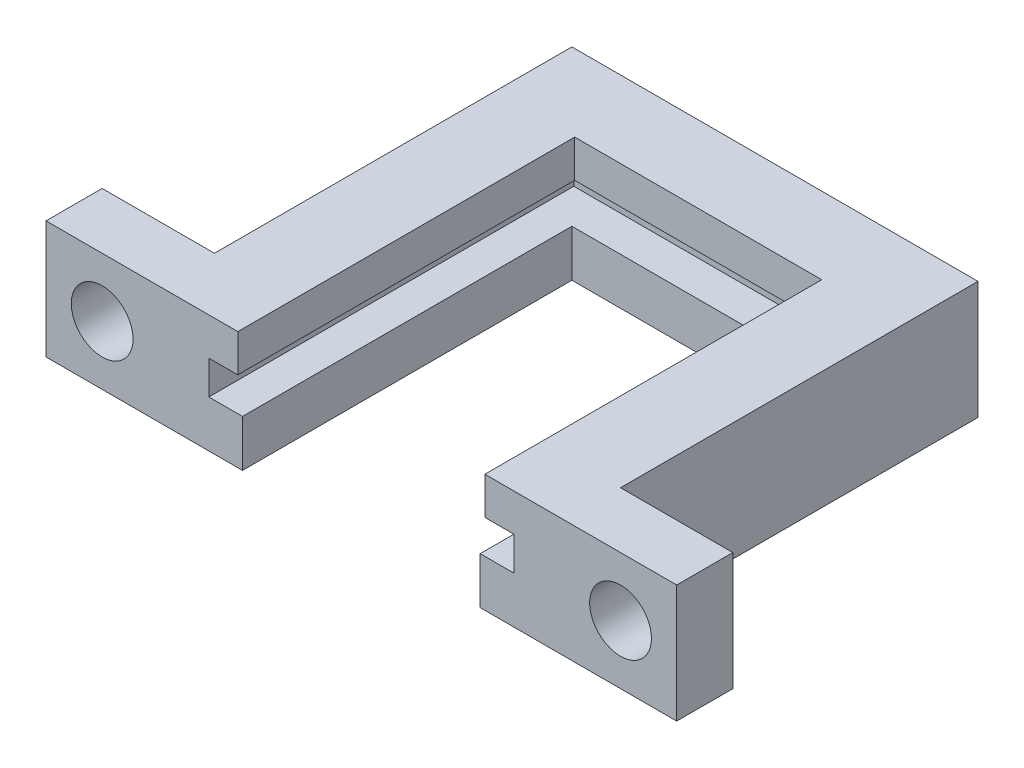
SolidWorks part; units mm, degrees
ref_plane "Front Plane" through (0, 0, 0) normal (0, 0, 1) x (1, 0, 0)
ref_plane "Top Plane" through (0, 0, 0) normal (0, 1, 0) x (1, 0, 0)
ref_plane "Right Plane" through (0, 0, 0) normal (1, 0, 0) x (0, 0, -1)
sketch "Sketch1" plane through (0, 0, 0) normal (0, 1, 0) x (1, 0, 0)
  line L0 (0, 0) -> (0, 22.1)
  line L1 (0, 22.1) -> (21.7, 22.1)
  line L2 (21.7, 22.1) -> (21.7, 0)
  line L3 (21.7, 0) -> (17.2, 0)
  line L4 (17.2, 0) -> (17.2, 17.6)
  line L5 (17.2, 17.6) -> (4.5, 17.6)
  line L6 (4.5, 17.6) -> (4.5, 0)
  line L7 (4.5, 0) -> (0, 0)
  dimension "D1" = 4.5
  dimension "D2" = 12.7
  dimension "D3" = 4.5
  dimension "D4" = 4.5
  dimension "D5" = 17.6
extrude "Boss-Extrude2" add sketch "Sketch1" along normal blind 2.5
sketch "Sketch3" plane through (0, 2.5, 0) normal (0, 1, 0) x (1, 0, 0)
  line L0 (0, 0) -> (0, 22.1)
  line L1 (0, 22.1) -> (21.7, 22.1)
  line L2 (21.7, 22.1) -> (21.7, 0)
  line L3 (21.7, 0) -> (19, 0)
  line L4 (17.2, 0) -> (21.7, 0) construction
  line L5 (19, 0) -> (19, 19.5)
  line L6 (19, 19.5) -> (2.7, 19.5)
  line L7 (2.7, 19.5) -> (2.7, 0)
  line L8 (0, 0) -> (4.5, 0) construction
  line L9 (2.7, 0) -> (0, 0)
  dimension "D1" = 16.3
  dimension "D2" = 19.5
  dimension "D3" = 2.7
extrude "Boss-Extrude3" add sketch "Sketch3" along normal blind 1.8
sketch "Sketch4" plane through (0, 4.3, 0) normal (0, 1, 0) x (1, 0, 0)
  line L0 (0, 0) -> (0, 22.1)
  line L1 (0, 22.1) -> (21.7, 22.1)
  line L2 (21.7, 22.1) -> (21.7, 0)
  line L3 (21.7, 0) -> (17.45, 0)
  line L4 (17.2, 0) -> (19, 0) construction
  line L5 (17.45, 0) -> (17.45, 18)
  line L6 (17.45, 18) -> (4.25, 18)
  line L7 (4.25, 18) -> (4.25, 0)
  line L8 (2.7, 0) -> (4.5, 0) construction
  line L9 (4.25, 0) -> (0, 0)
  dimension "D1" = 13.2
  dimension "D2" = 4.25
  dimension "D3" = 18
extrude "Boss-Extrude4" add sketch "Sketch4" along normal blind 2
sketch "Sketch6" plane through (0, 0, 0) normal (0, 0, 1) x (1, 0, 0)
  line L1 (0, 0) -> (-6, 0)
  line L2 (0, 0) -> (0, 6.3)
  line L3 (0, 6.3) -> (-6, 6.3)
  line L4 (-6, 0) -> (-6, 6.3)
  line L6 (21.7, 0) -> (27.7, 0)
  line L7 (21.7, 0) -> (21.7, 6.3)
  line L8 (21.7, 6.3) -> (27.7, 6.3)
  line L9 (27.7, 0) -> (27.7, 6.3)
  circle A0 centre (-3, 3.15) radius 1.65
  circle A1 centre (24.7, 3.15) radius 1.65
  dimension "D5" = 3.3
  dimension "D6" = 3.3
  dimension "D7" = 3.15
  dimension "D8" = 3
  dimension "D9" = 3
  dimension "D10" = 3.15
  dimension "D1" = 6
  dimension "D2" = 6.3
  dimension "D3" = 6
  dimension "D4" = 6.3
extrude "Boss-Extrude6" add sketch "Sketch6" against normal blind 3
